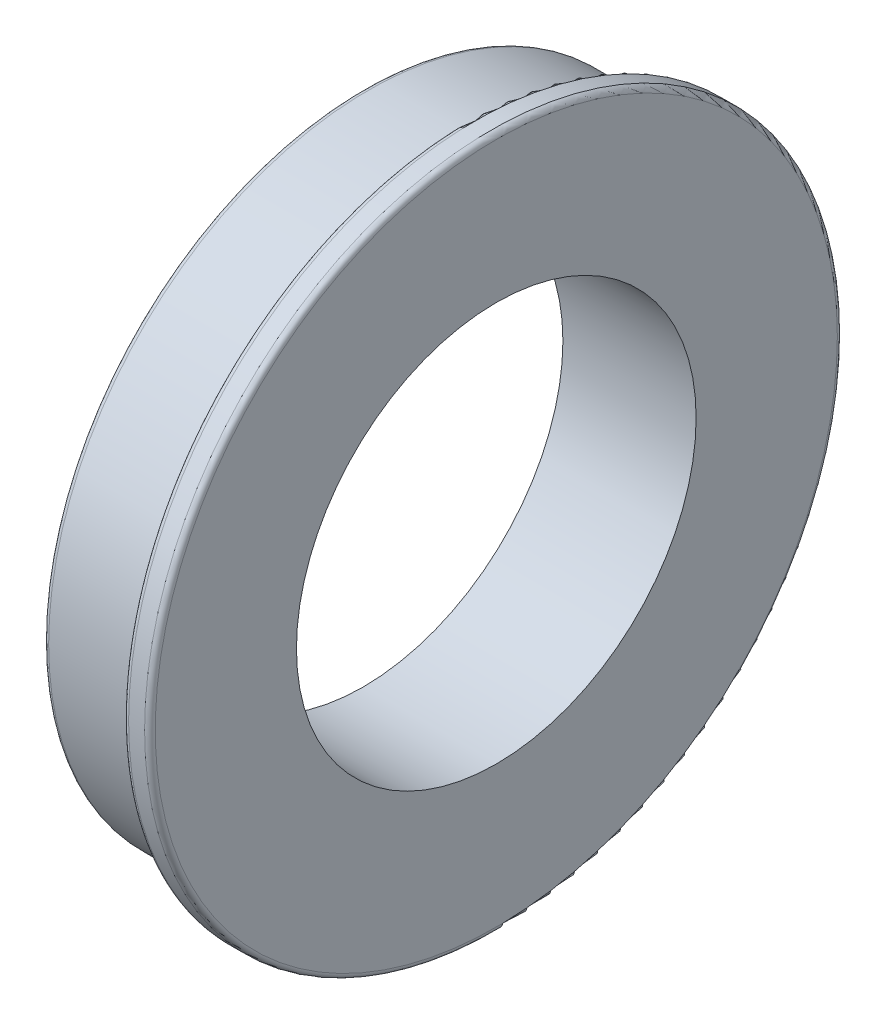
SolidWorks part; units mm, degrees
material "AISI 类型 A2 刀具钢"
ref_plane "前视基准面" through (0, 0, 0) normal (0, 0, 1) x (1, 0, 0)
ref_plane "上视基准面" through (0, 0, 0) normal (0, 1, 0) x (1, 0, 0)
ref_plane "右视基准面" through (0, 0, 0) normal (1, 0, 0) x (0, 0, -1)
sketch "草图1" plane through (0, 0, 0) normal (1, 0, 0) x (0, 0, -1)
  circle A0 centre (0, 0) radius 12
  circle A1 centre (0, 0) radius 7.5 construction
  dimension "D1" = 24
  dimension "D2" = 15
extrude "凸台-拉伸1" add sketch "草图1" along normal blind 4
sketch "草图2" plane through (4, 0, 0) normal (1, 0, 0) x (0, 0, -1)
  circle A0 centre (0, 0) radius 13
  dimension "D1" = 26
extrude "凸台-拉伸2" add sketch "草图2" along normal blind 1
sketch "草图3" plane through (0, 0, 0) normal (-1, 0, 0) x (0, 0, 1)
  circle A0 centre (0, 0) radius 7.5
  dimension "D1" = 15
extrude "切除-拉伸1" cut sketch "草图3" against normal through all
fillet "圆角1" radius 0.2 3 edges at (0, 0, -12) (5, 0, -13) (4, 0, -13)
